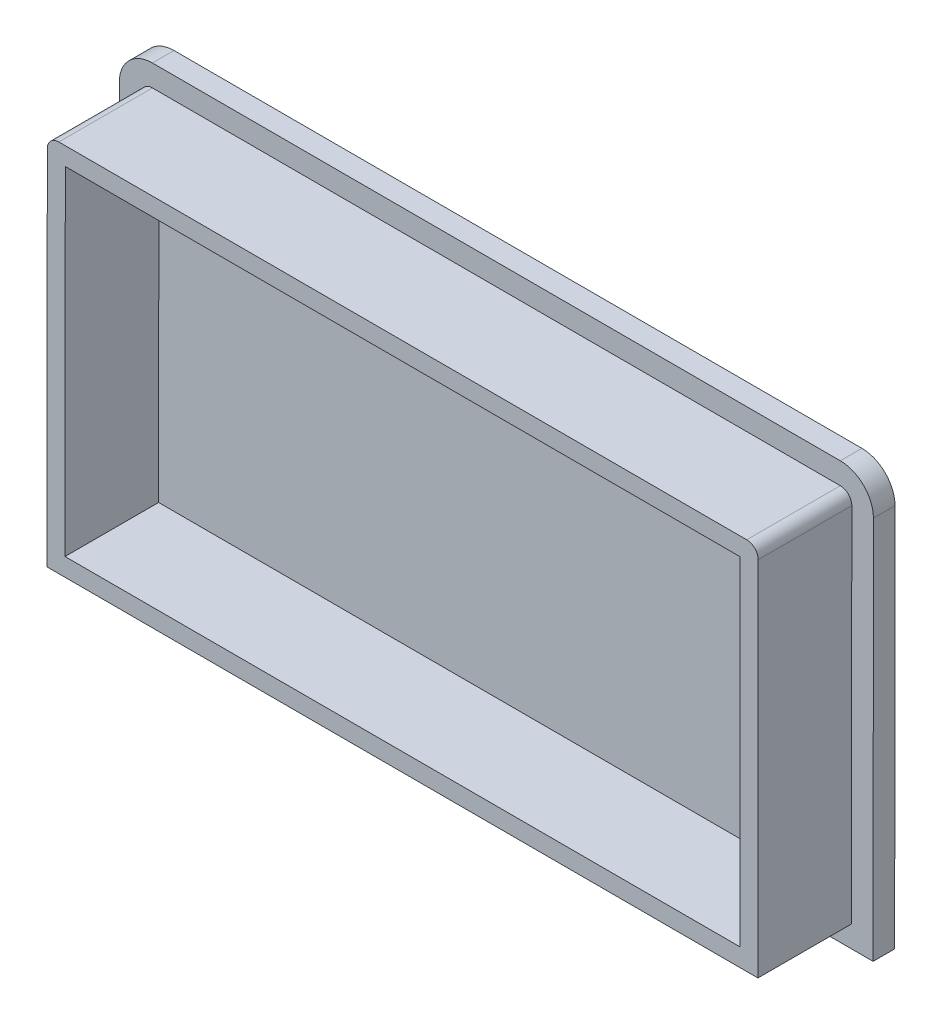
SolidWorks part; units mm, degrees
ref_plane "Front Plane" through (0, 0, 0) normal (0, 0, 1) x (1, 0, 0)
ref_plane "Top Plane" through (0, 0, 0) normal (0, 1, 0) x (1, 0, 0)
ref_plane "Right Plane" through (0, 0, 0) normal (1, 0, 0) x (0, 0, -1)
sketch "Esboço1" plane through (0, 0, 0) normal (0, 0, 1) x (1, 0, 0)
  line L0 (-108.7468, 5.9891) -> (-15.0024, 5.9123)
  line L1 (-15.0024, 5.9123) -> (-14.964, 52.8485)
  line L2 (-14.964, 52.8485) -> (-108.7083, 52.9253)
  line L3 (-108.7083, 52.9253) -> (-108.7468, 5.9891)
  line L12 (-111.2488, 3.4912) -> (-12.5045, 3.4102)
  line L13 (-12.5045, 3.4102) -> (-12.4632, 53.7464)
  line L14 (-14.0619, 55.3477) -> (-109.6063, 55.426)
  line L15 (-111.2076, 53.8273) -> (-111.2488, 3.4912)
  arc A0 (-14.964, 52.8485) -> (-14.964, 52.8485) centre (-14.964, 52.8485) ccw
  arc A1 (-108.7083, 52.9253) -> (-108.7083, 52.9253) centre (-108.7083, 52.9253) ccw
  arc A2 (-12.4632, 53.7464) -> (-14.0619, 55.3477) centre (-14.0632, 53.7477) ccw
  arc A3 (-109.6063, 55.426) -> (-111.2076, 53.8273) centre (-109.6076, 53.826) ccw
  dimension "D1" = 2.5
extrude "Ressalto-extrusão1" add sketch "Esboço1" along normal blind 13
sketch "Esboço2" plane through (0, 0, 0) normal (0, 0, -1) x (-1, 0, 0)
  line L8 (9.4632, 53.744) -> (9.5069, 0.4078)
  line L9 (9.5069, 0.4078) -> (114.2513, 0.4936)
  line L10 (114.2513, 0.4936) -> (114.2076, 53.8298)
  line L11 (109.6038, 58.426) -> (14.0595, 58.3477)
  line L12 (9.4632, 53.744) -> (9.5069, 0.4078)
  line L13 (9.5069, 0.4078) -> (114.2513, 0.4936)
  line L14 (114.2513, 0.4936) -> (114.2076, 53.8298)
  line L15 (109.6038, 58.426) -> (14.0595, 58.3477)
  arc A4 (114.2076, 53.8298) -> (109.6038, 58.426) centre (109.6076, 53.826) ccw
  arc A5 (14.0595, 58.3477) -> (9.4632, 53.744) centre (14.0632, 53.7477) ccw
  arc A6 (114.2076, 53.8298) -> (109.6038, 58.426) centre (109.6076, 53.826) ccw
  arc A7 (14.0595, 58.3477) -> (9.4632, 53.744) centre (14.0632, 53.7477) ccw
  dimension "D1" = 3
extrude "Ressalto-extrusão2" add sketch "Esboço2" along normal blind 3
